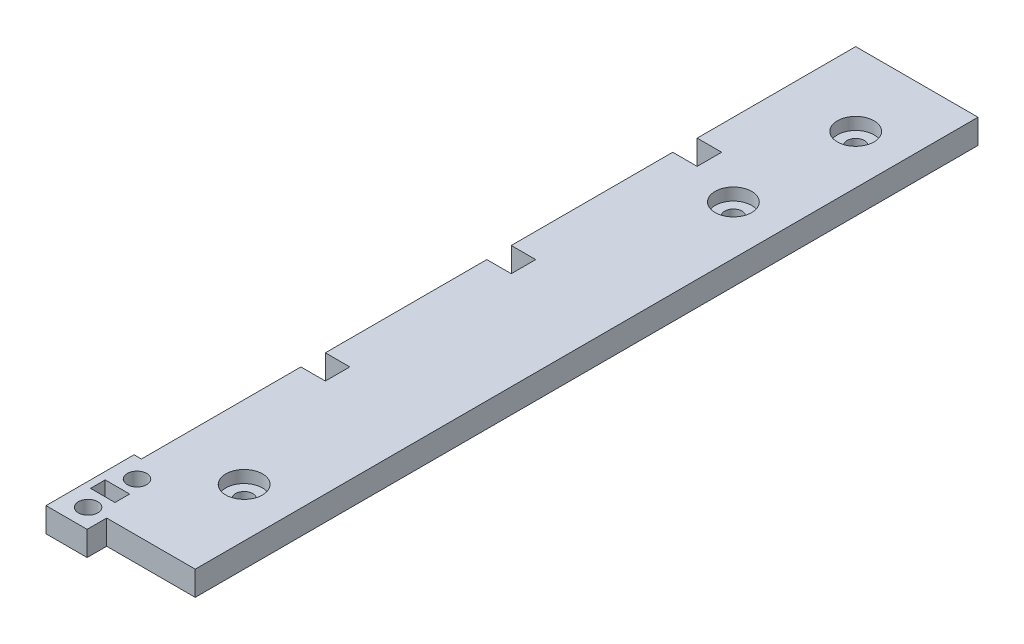
SolidWorks part; units mm, degrees
ref_plane "Front Plane" through (0, 0, 0) normal (0, 0, 1) x (1, 0, 0)
ref_plane "Top Plane" through (0, 0, 0) normal (0, 1, 0) x (1, 0, 0)
ref_plane "Right Plane" through (0, 0, 0) normal (1, 0, 0) x (0, 0, -1)
sketch "Sketch1" plane through (0, 0, 0) normal (0, 1, 0) x (1, 0, 0)
  line L8 (8.763, -10.3314) -> (8.763, -15.4114)
  line L11 (0, 192.8686) -> (31.75, 192.8686)
  line L12 (31.75, -10.3314) -> (31.75, 192.8686)
  line L13 (8.763, -15.4114) -> (-1.905, -15.4114)
  line L14 (-1.905, -15.4114) -> (-1.905, 7.4486)
  line L15 (-1.905, 7.4486) -> (0, 7.4486)
  line L16 (8.763, -10.3314) -> (31.75, -10.3314)
  line L17 (0, 7.4486) -> (0, 192.8686)
  dimension "D1" = 31.75
  dimension "D2" = 203.2
  dimension "D3" = 1.905
  dimension "D4" = 22.86
  dimension "D5" = 8.763
  dimension "D6" = 5.08
extrude "Boss-Extrude1" add sketch "Sketch1" along normal blind 6.35
sketch "Sketch2" plane through (0, 6.35, 0) normal (0, 1, 0) x (1, 0, 0)
  line L0 (0, 192.8686) -> (0, 7.4486) construction
  line L1 (0, 55.2006) -> (6.35, 55.2006)
  line L2 (0, 55.2006) -> (0, 48.8506)
  line L3 (0, 48.8506) -> (6.35, 48.8506)
  line L4 (6.35, 55.2006) -> (6.35, 48.8506)
  line L6 (0, 103.4606) -> (6.35, 103.4606)
  line L7 (0, 103.4606) -> (0, 97.1106)
  line L8 (0, 97.1106) -> (6.35, 97.1106)
  line L9 (6.35, 103.4606) -> (6.35, 97.1106)
  line L10 (0, 151.7206) -> (6.35, 151.7206)
  line L11 (0, 151.7206) -> (0, 145.3706)
  line L12 (0, 145.3706) -> (6.35, 145.3706)
  line L13 (6.35, 151.7206) -> (6.35, 145.3706)
  line L15 (8.763, -10.3314) -> (31.75, -10.3314) construction
  dimension "D1" = 6.35
  dimension "D2" = 6.35
  dimension "D3" = 6.35
  dimension "D4" = 6.35
  dimension "D5" = 59.182
  dimension "D6" = 6.35
  dimension "D7" = 6.35
  dimension "D8" = 41.91
  dimension "D9" = 41.91
extrude "Cut-Extrude1" cut sketch "Sketch2" against normal through all
hole_wizard "#8 (0.199) Diameter Hole1" positions "Sketch3" profile "Sketch4" hole size "#8" standard "ANSI Inch" end condition through all
sketch "Sketch3" plane through (0, 6.35, 0) normal (0, 1, 0) x (1, 0, 0)
  line L0 (-1.905, 7.4486) -> (-1.905, -15.4114) construction
  line L1 (0, 7.4486) -> (-1.905, 7.4486) construction
  point P0 (3.937, 2.3686)
  point P2 (3.937, -10.3314)
  dimension "D1" = 5.842
  dimension "D2" = 5.08
  dimension "D3" = 12.7
sketch "Sketch4" plane through (3.937, 6.35, -2.3686) normal (1, 0, 0) x (0, 0, 1)
  line L0 (0, 0) -> (0, 6.35)
  line L1 (0, 6.35) -> (2.5273, 6.35)
  line L2 (2.5273, 6.35) -> (2.5273, 0)
  line L5 (2.5273, 0) -> (0, 0)
  line L11 (0, -6.35) -> (0, 107.95) construction
  dimension "Thru Hole Dia." = 5.0546
  dimension "Thru Hole Depth" = 6.35
sketch "Sketch5" plane through (0, 6.35, 0) normal (0, 1, 0) x (1, 0, 0)
  line L0 (0, 7.4486) -> (0, -15.4114) construction
  line L1 (-1.905, -15.4114) -> (8.763, -15.4114) construction
  line L2 (0, -1.9494) -> (6.35, -1.9494)
  line L3 (6.35, -1.9494) -> (6.35, -5.7594)
  line L4 (6.35, -5.7594) -> (0, -5.7594)
  line L5 (8.763, -10.3314) -> (31.75, -10.3314) construction
  line L6 (0, -5.7594) -> (0, -1.9494)
  dimension "D1" = 4.572
  dimension "D2" = 6.35
  dimension "D3" = 3.81
extrude "Cut-Extrude2" cut sketch "Sketch5" against normal through all
hole_wizard "CBORE for #8 Binding Head Machine Screw1" positions "Sketch6" profile "Sketch7" counterbore size "#8" standard "ANSI Inch" end condition through all
sketch "Sketch6" plane through (0, 6.35, 0) normal (0, 1, 0) x (1, 0, 0)
  line L0 (31.75, 192.8686) -> (0, 192.8686) construction
  line L1 (31.75, -10.3314) -> (31.75, 192.8686) construction
  point P0 (19.05, 173.8186)
  point P2 (19.05, 142.0686)
  point P4 (19.05, 15.0686)
  dimension "D1" = 19.05
  dimension "D2" = 50.8
  dimension "D3" = 12.7
  dimension "D4" = 177.8
sketch "Sketch7" plane through (19.05, 6.35, -173.8186) normal (1, 0, 0) x (0, 0, 1)
  line L0 (0, 0) -> (0, 6.35)
  line L1 (0, 6.35) -> (2.2479, 6.35)
  line L3 (2.2479, 6.35) -> (2.2479, 3.175)
  line L4 (2.2479, 3.175) -> (4.7625, 3.175)
  line L5 (4.7625, 3.175) -> (4.7625, 0)
  line L7 (4.7625, 0) -> (0, 0)
  line L11 (0, -6.35) -> (0, 107.95) construction
  dimension "Thru Hole Dia." = 4.4958
  dimension "Thru Hole Depth" = 6.35
  dimension "C'Bore Dia." = 9.525
  dimension "C'Bore Depth" = 3.175
